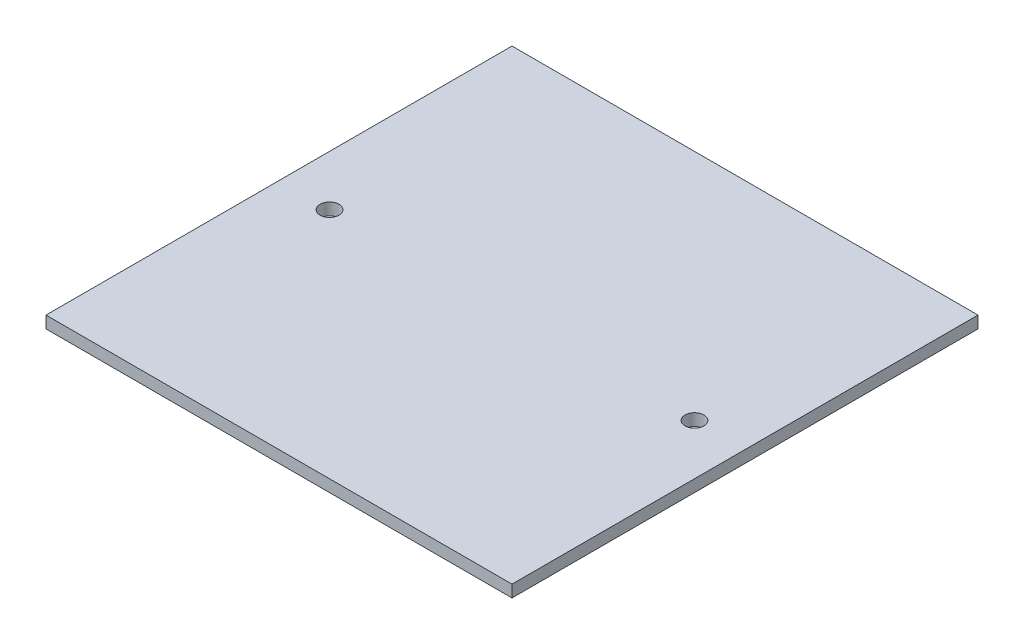
SolidWorks part; units mm, degrees
ref_plane "Alzado" through (0, 0, 0) normal (0, 0, 1) x (1, 0, 0)
ref_plane "Planta" through (0, 0, 0) normal (0, 1, 0) x (1, 0, 0)
ref_plane "Vista lateral" through (0, 0, 0) normal (1, 0, 0) x (0, 0, -1)
sketch "Croquis1" plane through (0, 0, 0) normal (0, 1, 0) x (1, 0, 0)
  line L1 (-36.9, 36.9) -> (36.9, 36.9)
  line L2 (-36.9, 36.9) -> (-36.9, -36.9)
  line L3 (-36.9, -36.9) -> (36.9, -36.9)
  line L4 (36.9, 36.9) -> (36.9, -36.9)
  line L5 (-36.9, 36.9) -> (36.9, -36.9) construction
  line L6 (-36.9, -36.9) -> (36.9, 36.9) construction
  point P0 (0, 0)
  dimension "D1" = 73.8
  dimension "D2" = 73.8
extrude "Saliente-Extruir3" add sketch "Croquis1" along normal blind 1.9
sketch "Croquis2" plane through (0, 1.9, 0) normal (0, 1, 0) x (1, 0, 0)
  line L0 (36.9, 0) -> (-36.9, 0) construction
  line L1 (36.9, -36.9) -> (36.9, 36.9) construction
  line L2 (-36.9, 36.9) -> (-36.9, -36.9) construction
  line L3 (0, 0) -> (0, 25.6728) construction
  circle A0 centre (-28.9, 0) radius 1.5
  circle A1 centre (28.9, 0) radius 1.5
  dimension "D1" = 3
  dimension "D2" = 8
extrude "Cortar-Extruir1" cut sketch "Croquis2" against normal through all both
